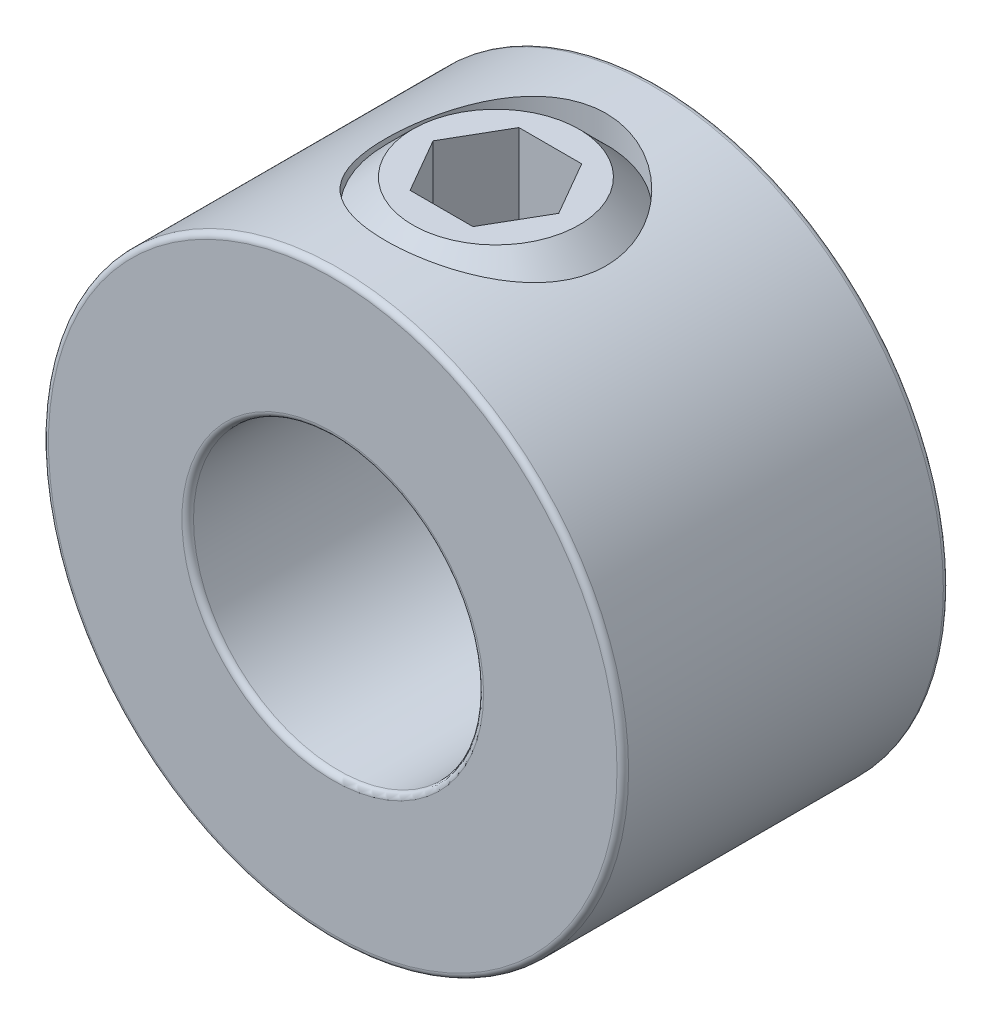
SolidWorks part; units mm, degrees
material "Cast Carbon Steel"
ref_plane "Front Plane" through (0, 0, 0) normal (0, 0, 1) x (1, 0, 0)
ref_plane "Top Plane" through (0, 0, 0) normal (0, 1, 0) x (1, 0, 0)
ref_plane "Right Plane" through (0, 0, 0) normal (1, 0, 0) x (0, 0, -1)
sketch "Sketch1" plane through (0, 0, 0) normal (0, 0, 1) x (1, 0, 0)
  circle A0 centre (0, 0) radius 6.35
  circle A1 centre (0, 0) radius 3.175
  point P4 (6.35, 0)
  dimension "Bore Dia" = 6.35
  dimension "OD" = 12.7
extrude "Extrude1" add sketch "Sketch1" along normal mid plane 7.1437
sketch "Sketch2" plane through (41.275, 0, 0) normal (0, -1, 0) x (0, 0, -1)
  line L0 (3.5719, -41.275) -> (-3.5719, -41.275) construction
  line L1 (-3.5719, -34.925) -> (-3.5719, -47.625) construction
  line L2 (3.5719, -47.625) -> (3.5719, -34.925) construction
  circle A0 centre (0, -41.275) radius 2.413
  point P7 (0, -43.688)
  dimension "Set Screw Dia" = 4.826
extrude "Cut-Extrude1" cut sketch "Sketch2" against normal through all
fillet "Fillet1" radius 0.127 4 edges at (3.175, 0, -3.5719) (3.175, 0, 3.5719) (6.35, 0, -3.5719) (6.35, 0, 3.5719)
sketch "Sketch3" plane through (0, 0, 0) normal (0, 0, 1) x (1, 0, 0)
  line L0 (-1.8198, 3.175) -> (-0.7119, 3.175)
  line L1 (0, 3.8869) -> (-0.7119, 3.175)
  line L2 (0, 3.8869) -> (0, 6.35)
  line L3 (0, 6.35) -> (-1.8198, 6.35)
  line L4 (-2.413, 3.7682) -> (-2.413, 5.7568)
  line L5 (0, 3.175) -> (0, 0) construction
  line L6 (-2.413, 3.7682) -> (-2.413, 3.175) construction
  line L7 (-2.413, 3.175) -> (-1.8198, 3.175) construction
  line L8 (-2.413, 5.7568) -> (-2.413, 6.35) construction
  line L9 (-1.8198, 3.175) -> (-2.413, 3.7682)
  line L10 (-2.413, 5.7568) -> (-1.8198, 6.35)
  line L11 (-2.413, 6.35) -> (-1.8198, 6.35) construction
  line L12 (-0.7119, 3.175) -> (0, 3.175) construction
  line L13 (0, 3.175) -> (0, 3.8869) construction
  circle A1 centre (0, 0) radius 3.175 construction
  dimension "Screw Length" = 3.175
  dimension "D2" = 0.5932
  dimension "D1" = 0.7119
revolve "Revolve1" add sketch "Sketch3" angle 360 about L5
sketch "Sketch4" plane through (3.3734, 6.35, 0) normal (0, -1, 0) x (0, 0, -1)
  line L1 (0, -1.9986) -> (-1.1906, -2.686)
  line L2 (-1.1906, -2.686) -> (-1.1906, -4.0608)
  line L3 (-1.1906, -4.0608) -> (0, -4.7483)
  line L4 (0, -4.7483) -> (1.1906, -4.0608)
  line L5 (1.1906, -4.0608) -> (1.1906, -2.686)
  line L6 (1.1906, -2.686) -> (0, -1.9986)
  circle A0 centre (0, -3.3734) radius 1.1906 construction
  circle A1 centre (0, -3.3734) radius 1.3748 construction
  dimension "D1" = 2.7496
  dimension "Hex Size" = 2.3813
extrude "Cut-Extrude2" cut sketch "Sketch4" along normal blind 2.3813
equation "\"D1@Fillet1\" = \"OD@Sketch1\"*.01"
equation "\"D1@Cut-Extrude2\" = \"Hex Size@Sketch4\""
equation "\"D2@Sketch3\" =(\"Set Screw Dia@Sketch2\"-\"D1@Sketch4\")/3.5"
equation "\"D1@Sketch3\" = \"D2@Sketch3\"*1.2"
